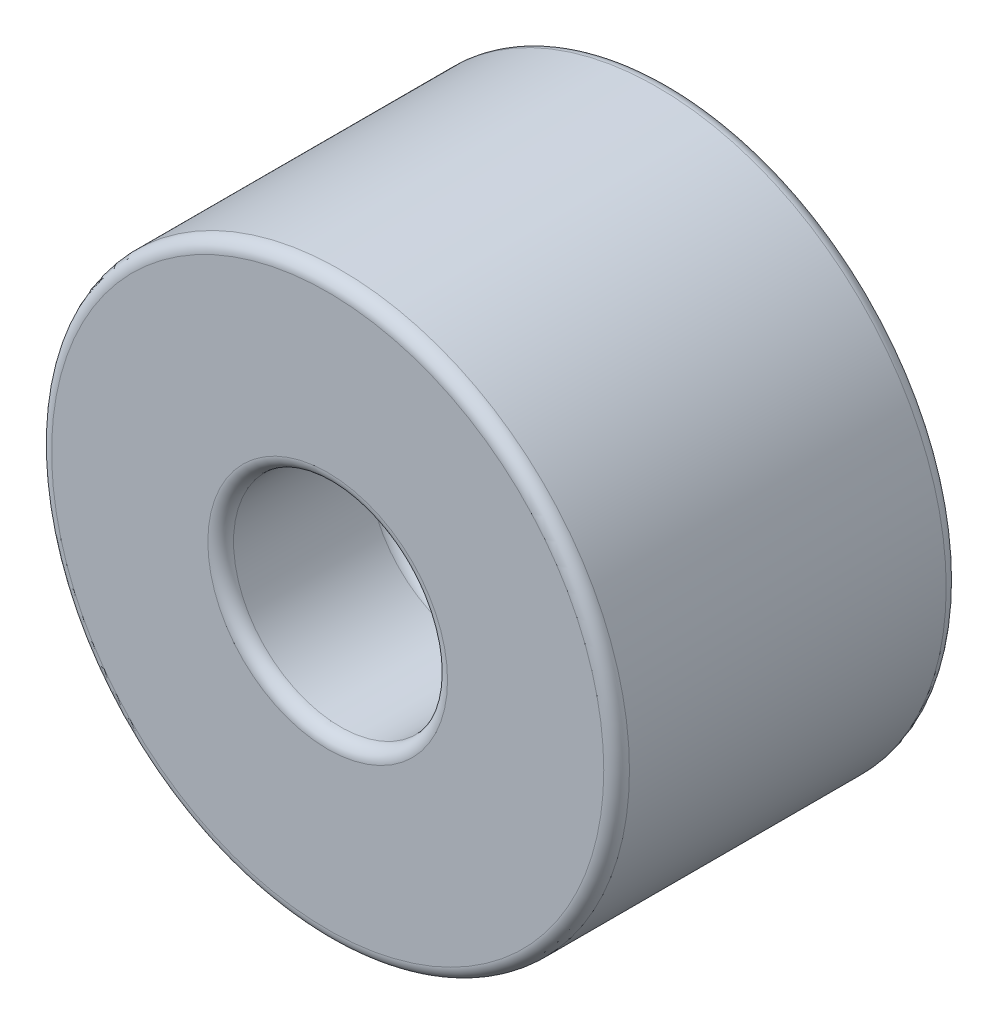
SolidWorks part; units mm, degrees
ref_plane "Front Plane" through (0, 0, 0) normal (0, 0, 1) x (1, 0, 0)
ref_plane "Top Plane" through (0, 0, 0) normal (0, 1, 0) x (1, 0, 0)
ref_plane "Right Plane" through (0, 0, 0) normal (1, 0, 0) x (0, 0, -1)
sketch "Sketch1" plane through (0, 0, 0) normal (0, 0, 1) x (1, 0, 0)
  circle A1 centre (0, 0) radius 135
  dimension "D1" = 270
extrude "Boss-Extrude2" add sketch "Sketch1" along normal blind 160
sketch "Sketch3" plane through (0, 0, 160) normal (0, 0, 1) x (1, 0, 0)
  circle A0 centre (0, 0) radius 50
extrude "Cut-Extrude1" cut sketch "Sketch3" against normal blind 75
sketch "Sketch4" plane through (0, 0, 0) normal (0, 0, -1) x (-1, 0, 0)
  circle A0 centre (0, 0) radius 50
extrude "Cut-Extrude2" cut sketch "Sketch4" against normal blind 75
fillet "Fillet1" radius 6 6 edges at (50, 0, 160) (50, 0, 85) (-50, 0, 0) (135, 0, 0) (135, 0, 160) (-50, 0, 75)
sketch "Sketch5" plane through (0, 0, 85) normal (0, 0, 1) x (1, 0, 0)
  line L0 (0, 0) -> (44, 0) construction
  circle A0 centre (0, 0) radius 44 construction
  circle A1 centre (35, 0) radius 4
  circle A2 centre (-17.5, -30.3109) radius 4
  circle A3 centre (-17.5, 30.3109) radius 4
  point P5 (35, 0)
  point P14 (0, 0)
  point P15 (0, 0)
  dimension "D1" = 35
  dimension "D2" = 8
  dimension "D3" = 3
extrude "Cut-Extrude3" cut sketch "Sketch5" against normal blind 45
sketch "Sketch6" plane through (0, 0, 85) normal (0, 0, 1) x (1, 0, 0)
  circle A0 centre (0, 0) radius 6.5
  dimension "D1" = 13
extrude "Cut-Extrude4" cut sketch "Sketch6" against normal through all
